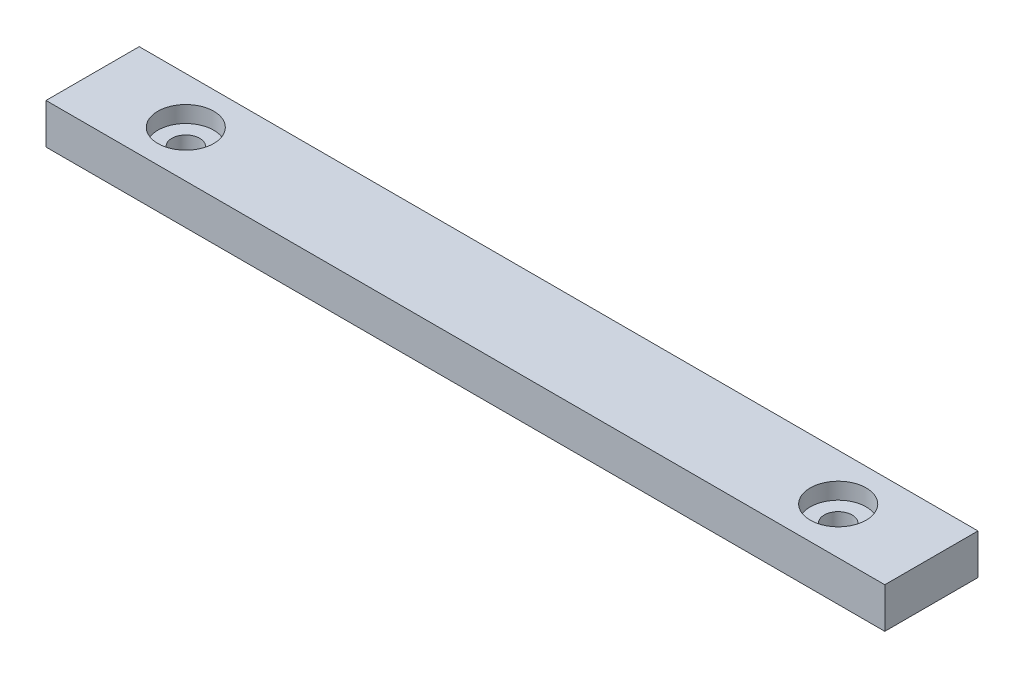
SolidWorks part; units mm, degrees
ref_plane "Front Plane" through (0, 0, 0) normal (0, 0, 1) x (1, 0, 0)
ref_plane "Top Plane" through (0, 0, 0) normal (0, 1, 0) x (1, 0, 0)
ref_plane "Right Plane" through (0, 0, 0) normal (1, 0, 0) x (0, 0, -1)
sketch "Sketch1" plane through (0, 0, 0) normal (0, 1, 0) x (1, 0, 0)
  line L1 (-135, -15) -> (135, -15)
  line L2 (-135, -15) -> (-135, 15)
  line L3 (-135, 15) -> (135, 15)
  line L4 (135, -15) -> (135, 15)
  line L5 (-135, -15) -> (135, 15) construction
  line L6 (-135, 15) -> (135, -15) construction
  point P0 (0, 0)
  dimension "D1" = 270
  dimension "D2" = 30
extrude "Boss-Extrude1" add sketch "Sketch1" along normal blind 13
sketch "Sketch2" plane through (0, 13, 0) normal (0, 1, 0) x (1, 0, 0)
  circle A0 centre (-105, 0) radius 5
  circle A1 centre (105, 0) radius 5
hole_wizard "CBORE for M8 Hex Head Bolt1" positions "3DSketch1" profile "Sketch3" counterbore size "M8" standard "ISO"
sketch3d "3DSketch1"
  point P0 (-105, 13, 0)
  point P3 (105, 13, 0)
sketch "Sketch3" plane through (-105, 13, 0) normal (1, 0, 0) x (0, 0, 1)
  line L0 (0, 0) -> (0, 17.7039)
  line L1 (0, 17.7039) -> (4.5, 15)
  line L2 (4.5, 15) -> (4.5, 5.3)
  line L3 (4.5, 5.3) -> (9.0055, 5.3)
  line L4 (9.0055, 5.3) -> (9.0055, 0)
  line L5 (9.0055, 0) -> (0, 0)
  line L10 (0, 17.7039) -> (-4.5, 15) construction
  line L11 (0, -6.35) -> (0, 107.95) construction
  dimension "Hole Dia." = 9
  dimension "Hole Depth" = 15
  dimension "C'Bore Dia." = 18.011
  dimension "C'Bore Depth" = 5.3
  dimension "Drill Angle" = 118
